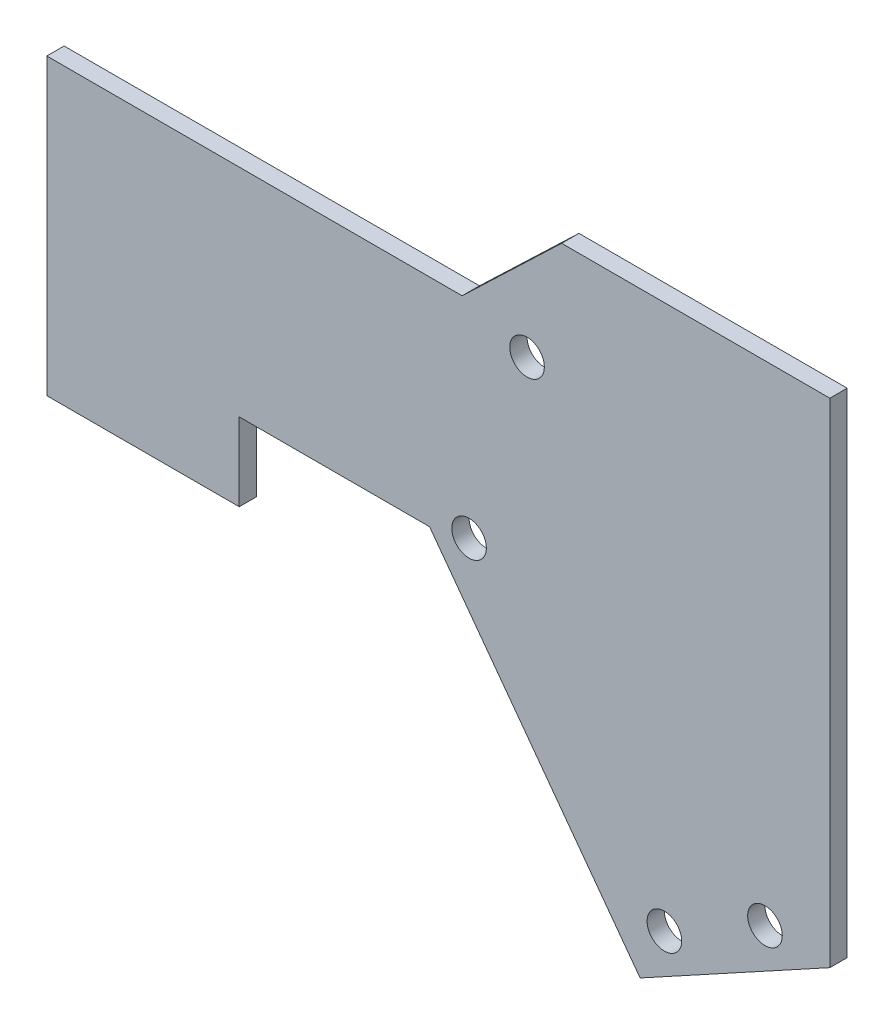
SolidWorks part; units mm, degrees
ref_plane "Front Plane" through (0, 0, 0) normal (0, 0, 1) x (1, 0, 0)
ref_plane "Top Plane" through (0, 0, 0) normal (0, 1, 0) x (1, 0, 0)
ref_plane "Right Plane" through (0, 0, 0) normal (1, 0, 0) x (0, 0, -1)
sketch "Sketch1" plane through (0, 0, 0) normal (0, 0, 1) x (1, 0, 0)
  line L0 (0, 0) -> (0, -361.95)
  line L1 (0, 0) -> (-196.85, 0)
  line L2 (-196.85, 0) -> (-269.875, -69.85)
  line L3 (-269.875, -69.85) -> (-574.675, -69.85)
  line L4 (-574.675, -69.85) -> (-574.675, -285.75)
  line L5 (0, -361.95) -> (-139.2664, -438.15)
  line L6 (-139.2664, -438.15) -> (-293.7685, -228.6)
  line L7 (-293.7685, -228.6) -> (-433.4685, -228.6)
  line L9 (-433.4685, -285.75) -> (-574.675, -285.75)
  line L10 (-433.4685, -228.6) -> (-433.4685, -285.75)
  line L11 (-574.675, -69.85) -> (-536.575, -69.85) construction
  line L12 (-574.675, -69.85) -> (-574.675, -158.75) construction
  line L13 (-574.675, -158.75) -> (-536.575, -158.75) construction
  line L14 (-536.575, -69.85) -> (-536.575, -158.75) construction
  circle A0 centre (-121.4362, -399.4406) radius 12.7
  circle A1 centre (-47.625, -359.0546) radius 12.7
  circle A2 centre (-264.8148, -221.3942) radius 12.7
  circle A3 centre (-222.25, -85.0069) radius 12.7
  point P11 (-433.4685, -285.75)
  point P23 (-260.8349, -222.5731)
  dimension "D12" = 25.4
  dimension "D15" = 84.1375
  dimension "D16" = 222.25
  dimension "D17" = 228.6
  dimension "D18" = 142.875
  dimension "D19" = 330.2
  dimension "D20" = 25.4
  dimension "D21" = 25.4
  dimension "D1" = 574.675
  dimension "D2" = 69.85
  dimension "D3" = 361.95
  dimension "D4" = 438.15
  dimension "D5" = 158.75
  dimension "D6" = 260.35
  dimension "D7" = 196.85
  dimension "D8" = 158.75
  dimension "D9" = 304.8
  dimension "D10" = 139.7
  dimension "D11" = 215.9
  dimension "D13" = 88.9
  dimension "D14" = 38.1
  dimension "D22" = 47.625
extrude "Boss-Extrude1" add sketch "Sketch1" along normal blind 12.7
